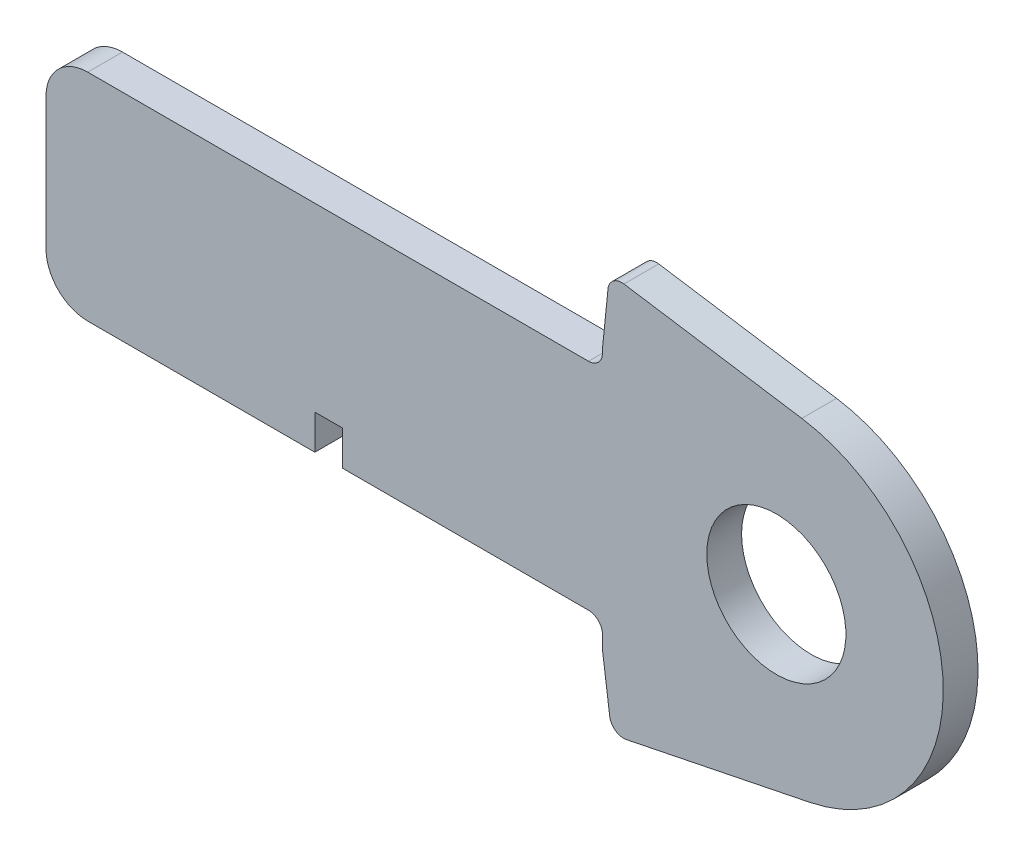
SolidWorks part; units mm, degrees
ref_plane "Front Plane" through (0, 0, 0) normal (0, 0, 1) x (1, 0, 0)
ref_plane "Top Plane" through (0, 0, 0) normal (0, 1, 0) x (1, 0, 0)
ref_plane "Right Plane" through (0, 0, 0) normal (1, 0, 0) x (0, 0, -1)
curve "Curve1"
  spline degree 3 poles (452.1031, 0.7048, 0) (452.0685, 0.7262, 0) (451.9301, 0.8117, 0) (451.6183, 1.003, 0) (451.099, 1.3216, 0) (450.372, 1.7653, 0) (449.438, 2.3329, 0) (448.2963, 3.0204, 0) (446.9478, 3.8257, 0) (445.3928, 4.7448, 0) (443.6314, 5.7736, 0) (441.6643, 6.9077, 0) (439.4916, 8.1409, 0) (437.1143, 9.468, 0) (434.5331, 10.8828, 0) (431.7485, 12.3789, 0) (428.7615, 13.9486, 0) (425.5733, 15.5853, 0) (422.1844, 17.2798, 0) (418.5964, 19.0251, 0) (414.8106, 20.8125, 0) (410.8282, 22.6325, 0) (406.6515, 24.4776, 0) (402.2816, 26.3365, 0) (397.7212, 28.201, 0) (392.972, 30.0605, 0) (388.0369, 31.9065, 0) (382.9178, 33.7272, 0) (377.6186, 35.5144, 0) (372.1418, 37.2567, 0) (366.4913, 38.9446, 0) (360.6704, 40.5671, 0) (354.684, 42.1159, 0) (348.5359, 43.5797, 0) (342.2312, 44.9487, 0) (335.775, 46.2147, 0) (329.1727, 47.3651, 0) (322.4425, 48.3989, 0) (315.6929, 49.2588, 0) (308.9571, 50.1023, 0) (302.2314, 50.8946, 0) (295.4235, 51.6533, 0) (288.5399, 52.3742, 0) (281.5875, 53.055, 0) (274.5733, 53.6928, 0) (267.5046, 54.2857, 0) (260.3883, 54.8303, 0) (253.2318, 55.3259, 0) (246.0422, 55.768, 0) (238.8272, 56.1563, 0) (231.5941, 56.4881, 0) (224.3504, 56.7611, 0) (217.1039, 56.9737, 0) (209.862, 57.1238, 0) (202.6326, 57.2105, 0) (195.4232, 57.2315, 0) (188.2416, 57.1863, 0) (181.0954, 57.0734, 0) (173.9924, 56.8912, 0) (166.9401, 56.6395, 0) (159.9462, 56.3182, 0) (153.0184, 55.9248, 0) (146.164, 55.4618, 0) (139.3909, 54.9271, 0) (132.7063, 54.3206, 0) (126.1174, 53.645, 0) (119.6314, 52.8983, 0) (113.2554, 52.0826, 0) (106.9962, 51.1996, 0) (100.8609, 50.2488, 0) (94.8561, 49.2329, 0) (88.9882, 48.153, 0) (83.2635, 47.0122, 0) (77.6882, 45.8109, 0) (72.2682, 44.5525, 0) (67.0092, 43.2395, 0) (61.9167, 41.874, 0) (56.9959, 40.4594, 0) (52.2519, 38.999, 0) (47.6902, 37.4943, 0) (43.3141, 35.951, 0) (39.1291, 34.3702, 0) (35.1384, 32.7568, 0) (31.3466, 31.113, 0) (27.7567, 29.4439, 0) (24.3726, 27.7512, 0) (21.1967, 26.0397, 0) (18.2324, 24.3122, 0) (15.4823, 22.5717, 0) (12.9477, 20.8227, 0) (10.632, 19.0664, 0) (8.5361, 17.307, 0) (6.6613, 15.5474, 0) (5.0102, 13.7886, 0) (3.5829, 12.0339, 0) (2.3811, 10.2847, 0) (1.4051, 8.5424, 0) (0.6571, 6.8085, 0) (0.1363, 5.084, 0) (-0.1488, 3.3712, 0) (-0.2197, 1.669, 0) (-0.0731, 0.5555, 0) (0, 0, 0) knots 0 0 0 0 0.000254 0.001015 0.002283 0.004057 0.006331 0.009105 0.012374 0.016134 0.02038 0.025106 0.030306 0.035972 0.0421 0.048678 0.055702 0.06316 0.071046 0.07935 0.088063 0.097176 0.106678 0.116562 0.126814 0.137428 0.148394 0.1597 0.171338 0.183298 0.19557 0.208144 0.221012 0.234162 0.247587 0.261277 0.275223 0.289414 0.303771 0.317689 0.331784 0.34604 0.360444 0.374983 0.38964 0.404403 0.419257 0.434187 0.449177 0.464215 0.479284 0.49437 0.509458 0.524532 0.539579 0.554583 0.56953 0.584403 0.599191 0.613877 0.628447 0.642889 0.657186 0.671326 0.685294 0.699078 0.712665 0.726043 0.739198 0.752118 0.764792 0.777208 0.789356 0.801224 0.812804 0.824083 0.835055 0.84571 0.856038 0.866034 0.875689 0.884998 0.893953 0.902553 0.910789 0.918661 0.926166 0.933303 0.940071 0.946475 0.952518 0.958205 0.963547 0.968557 0.97325 0.977651 0.981787 0.985694 0.989415 0.993001 0.996508 1 1 1 1
curve "Curve2"
  spline degree 3 poles (0, 0, 0) (0.1161, -0.5481, 0) (0.3488, -1.6467, 0) (0.9811, -3.2283, 0) (1.8173, -4.7487, 0) (2.8749, -6.2038, 0) (4.147, -7.5932, 0) (5.6306, -8.9184, 0) (7.3243, -10.1787, 0) (9.226, -11.3735, 0) (11.3328, -12.5041, 0) (13.6425, -13.5697, 0) (16.1528, -14.5701, 0) (18.8611, -15.5039, 0) (21.764, -16.3724, 0) (24.8588, -17.1737, 0) (28.1419, -17.9088, 0) (31.6103, -18.5759, 0) (35.26, -19.1755, 0) (39.0874, -19.7075, 0) (43.0885, -20.172, 0) (47.2594, -20.5682, 0) (51.596, -20.8969, 0) (56.0938, -21.1583, 0) (60.7487, -21.3533, 0) (65.556, -21.481, 0) (70.5112, -21.5436, 0) (75.6096, -21.5419, 0) (80.8464, -21.4754, 0) (86.2171, -21.3479, 0) (91.7164, -21.1586, 0) (97.3395, -20.9096, 0) (103.0813, -20.6036, 0) (108.9365, -20.2416, 0) (114.9002, -19.8251, 0) (120.967, -19.3576, 0) (127.1315, -18.8401, 0) (133.3883, -18.2757, 0) (139.7319, -17.6673, 0) (146.1567, -17.0167, 0) (152.6572, -16.327, 0) (159.2275, -15.6004, 0) (165.862, -14.8409, 0) (172.5546, -14.0497, 0) (179.2998, -13.2315, 0) (186.0911, -12.3877, 0) (192.923, -11.5217, 0) (199.7891, -10.6375, 0) (206.6832, -9.7349, 0) (213.5994, -8.8205, 0) (220.5311, -7.8935, 0) (227.4721, -6.9586, 0) (234.4161, -6.0188, 0) (241.3564, -5.0743, 0) (248.2868, -4.1291, 0) (255.2009, -3.1857, 0) (262.0918, -2.2442, 0) (268.9535, -1.3094, 0) (275.779, -0.3811, 0) (282.5619, 0.5389, 0) (289.2958, 1.4477, 0) (295.9744, 2.3443, 0) (302.5907, 3.228, 0) (309.138, 4.0992, 0) (315.5119, 4.9314, 0) (321.6955, 5.769, 0) (327.7099, 6.4556, 0) (333.6493, 7.0417, 0) (339.52, 7.5222, 0) (345.315, 7.9041, 0) (351.0275, 8.19, 0) (356.6509, 8.3839, 0) (362.1779, 8.4917, 0) (367.6017, 8.516, 0) (372.9148, 8.4647, 0) (378.1105, 8.3417, 0) (383.1813, 8.1528, 0) (388.1203, 7.9042, 0) (392.9205, 7.6027, 0) (397.5745, 7.2527, 0) (402.076, 6.8625, 0) (406.4179, 6.4377, 0) (410.5937, 5.9833, 0) (414.5972, 5.5086, 0) (418.4221, 5.0169, 0) (422.0625, 4.5163, 0) (425.5126, 4.0117, 0) (428.7669, 3.5097, 0) (431.8204, 3.015, 0) (434.6681, 2.5342, 0) (437.3055, 2.0718, 0) (439.7281, 1.6323, 0) (441.9324, 1.2212, 0) (443.9143, 0.8406, 0) (445.6709, 0.4968, 0) (447.199, 0.1913, 0) (448.4964, -0.0716, 0) (449.5609, -0.2909, 0) (450.3908, -0.463, 0) (450.9844, -0.5881, 0) (451.3411, -0.6626, 0) (451.4997, -0.6964, 0) (451.5393, -0.7048, 0) knots 0 0 0 0 0.003638 0.007293 0.011028 0.014901 0.018963 0.023258 0.027821 0.032679 0.037853 0.043362 0.049215 0.055422 0.061989 0.068918 0.076211 0.083868 0.091887 0.100266 0.109 0.118085 0.127515 0.137285 0.147388 0.157816 0.168563 0.179619 0.190977 0.202627 0.21456 0.226767 0.239236 0.251959 0.264924 0.27812 0.291536 0.30516 0.318981 0.332985 0.347163 0.361499 0.375981 0.390597 0.405333 0.420175 0.43511 0.450124 0.465203 0.480333 0.495501 0.51069 0.525887 0.541078 0.556247 0.571382 0.586466 0.601485 0.616424 0.631269 0.646007 0.660621 0.675098 0.689423 0.703582 0.716908 0.730009 0.742952 0.755726 0.76832 0.780724 0.792927 0.804916 0.816679 0.828204 0.839475 0.850481 0.861208 0.871639 0.881763 0.891564 0.901027 0.910139 0.918884 0.927249 0.935221 0.942785 0.949928 0.956638 0.962904 0.968712 0.974054 0.978918 0.983297 0.98718 0.990561 0.993433 0.995791 0.99763 0.998946 0.999737 1 1 1 1
sketch "Sketch1" plane through (0, 0, 0) normal (0, 0, 1) x (1, 0, 0)
  line L24 (435.3301, 0.6787) -> (439.1729, -1.6142)
  line L25 (434.7872, -0.6787) -> (439.1729, -1.6142)
  spline S4 degree 3 poles (0, 0) (0.1118, -0.5277) (0.3359, -1.5856) (0.9447, -3.1085) (1.7499, -4.5725) (2.7683, -5.9736) (3.9931, -7.3115) (5.4217, -8.5876) (7.0526, -9.8011) (8.8837, -10.9516) (10.9124, -12.0402) (13.1363, -13.0663) (15.5535, -14.0296) (18.1613, -14.9287) (20.9565, -15.765) (23.9365, -16.5366) (27.0978, -17.2444) (30.4375, -17.8867) (33.9519, -18.4641) (37.6373, -18.9763) (41.49, -19.4236) (45.5061, -19.8051) (49.6818, -20.1216) (54.0128, -20.3734) (58.4949, -20.5611) (63.1239, -20.6841) (67.8952, -20.7443) (72.8045, -20.7427) (77.847, -20.6787) (83.0184, -20.5559) (88.3137, -20.3736) (93.7282, -20.1339) (99.2569, -19.8392) (104.895, -19.4906) (110.6374, -19.0896) (116.4791, -18.6394) (122.4149, -18.1411) (128.4396, -17.5977) (134.5478, -17.0118) (140.7343, -16.3853) (146.9936, -15.7212) (153.3201, -15.0216) (159.7085, -14.2903) (166.1528, -13.5285) (172.6478, -12.7406) (179.1872, -11.9281) (185.7655, -11.0942) (192.377, -10.2428) (199.0153, -9.3738) (205.6749, -8.4933) (212.3494, -7.6007) (219.0329, -6.7005) (225.7193, -5.7955) (232.4021, -4.886) (239.0753, -3.9759) (245.7329, -3.0675) (252.3682, -2.161) (258.9753, -1.2608) (265.5476, -0.3669) (272.0789, 0.5189) (278.563, 1.394) (284.9937, 2.2573) (291.3645, 3.1082) (297.669, 3.9471) (303.8064, 4.7484) (309.7606, 5.555) (315.5518, 6.2161) (321.2709, 6.7805) (326.9238, 7.2431) (332.5038, 7.6108) (338.0044, 7.8861) (343.4191, 8.0729) (348.7411, 8.1767) (353.9637, 8.2001) (359.0797, 8.1506) (364.0826, 8.0323) (368.9653, 7.8503) (373.7211, 7.6109) (378.3431, 7.3206) (382.8245, 6.9836) (387.159, 6.6079) (391.3398, 6.1989) (395.3607, 5.7613) (399.2157, 5.3043) (402.8986, 4.8308) (406.404, 4.3487) (409.7261, 3.8629) (412.8597, 3.3795) (415.7999, 2.9031) (418.5419, 2.4402) (421.0815, 1.9949) (423.4142, 1.5717) (425.5368, 1.1759) (427.445, 0.8095) (429.1365, 0.4784) (430.6079, 0.1842) (431.8572, -0.0689) (432.8822, -0.2801) (433.6813, -0.4458) (434.2529, -0.5663) (434.5964, -0.638) (434.749, -0.6706) (434.7872, -0.6787) knots 0 0 0 0 0.003638 0.007293 0.011028 0.014901 0.018963 0.023258 0.027821 0.032679 0.037853 0.043362 0.049215 0.055422 0.061989 0.068918 0.076211 0.083868 0.091887 0.100266 0.109 0.118085 0.127515 0.137285 0.147388 0.157816 0.168563 0.179619 0.190977 0.202627 0.21456 0.226767 0.239236 0.251959 0.264924 0.27812 0.291536 0.30516 0.318981 0.332985 0.347163 0.361499 0.375981 0.390597 0.405333 0.420175 0.43511 0.450124 0.465203 0.480333 0.495501 0.51069 0.525887 0.541078 0.556247 0.571382 0.586466 0.601485 0.616424 0.631269 0.646007 0.660621 0.675098 0.689423 0.703582 0.716908 0.730009 0.742952 0.755726 0.76832 0.780724 0.792927 0.804916 0.816679 0.828204 0.839475 0.850481 0.861208 0.871639 0.881763 0.891564 0.901027 0.910139 0.918884 0.927249 0.935221 0.942785 0.949928 0.956638 0.962904 0.968712 0.974054 0.978918 0.983297 0.98718 0.990561 0.993433 0.995791 0.99763 0.998946 0.999737 1 1 1 1
  spline S5 degree 3 poles (435.3301, 0.6787) (435.2968, 0.6993) (435.1635, 0.7816) (434.8632, 0.9658) (434.3632, 1.2726) (433.6632, 1.6998) (432.7638, 2.2463) (431.6645, 2.9084) (430.3661, 3.6837) (428.8687, 4.5688) (427.1727, 5.5594) (425.2785, 6.6514) (423.1865, 7.8389) (420.8974, 9.1168) (418.4119, 10.4791) (415.7306, 11.9197) (412.8545, 13.4311) (409.7845, 15.0071) (406.5213, 16.6387) (403.0665, 18.3192) (399.4211, 20.0403) (395.5865, 21.7928) (391.5647, 23.5695) (387.357, 25.3594) (382.9657, 27.1547) (378.3927, 28.9452) (373.6407, 30.7228) (368.7116, 32.4759) (363.609, 34.1968) (358.3353, 35.8745) (352.8945, 37.4998) (347.2896, 39.0621) (341.5252, 40.5534) (335.6052, 41.9629) (329.5344, 43.2811) (323.3177, 44.5002) (316.9603, 45.6079) (310.4799, 46.6033) (303.9807, 47.4313) (297.4948, 48.2435) (291.0186, 49.0064) (284.4633, 49.737) (277.8351, 50.4311) (271.1406, 51.0867) (264.3866, 51.7008) (257.5802, 52.2717) (250.7279, 52.7961) (243.8369, 53.2733) (236.914, 53.699) (229.9667, 54.0729) (223.0019, 54.3924) (216.027, 54.6553) (209.0493, 54.86) (202.0761, 55.0045) (195.1149, 55.088) (188.173, 55.1082) (181.2578, 55.0647) (174.3767, 54.956) (167.5373, 54.7806) (160.7467, 54.5381) (154.0122, 54.2288) (147.3414, 53.85) (140.7414, 53.4041) (134.2195, 52.8893) (127.7829, 52.3053) (121.4385, 51.6548) (115.1931, 50.9357) (109.0536, 50.1503) (103.0266, 49.3001) (97.119, 48.3846) (91.3369, 47.4064) (85.6868, 46.3665) (80.1745, 45.2681) (74.806, 44.1113) (69.5871, 42.8996) (64.5231, 41.6353) (59.6196, 40.3205) (54.8814, 38.9584) (50.3134, 37.5521) (45.9209, 36.1032) (41.7071, 34.6172) (37.6774, 33.0951) (33.8348, 31.5415) (30.1837, 29.9587) (26.7269, 28.3515) (23.4684, 26.7216) (20.4104, 25.0737) (17.5559, 23.4102) (14.9079, 21.7343) (12.4673, 20.0502) (10.2376, 18.359) (8.2194, 16.6649) (6.4142, 14.9706) (4.8244, 13.2771) (3.45, 11.5875) (2.2928, 9.9031) (1.353, 8.2255) (0.6327, 6.5559) (0.1312, 4.8953) (-0.1433, 3.2462) (-0.2116, 1.607) (-0.0704, 0.5349) (0, 0) knots 0 0 0 0 0.000254 0.001015 0.002283 0.004057 0.006331 0.009105 0.012374 0.016134 0.02038 0.025106 0.030306 0.035972 0.0421 0.048678 0.055702 0.06316 0.071046 0.07935 0.088063 0.097176 0.106678 0.116562 0.126814 0.137428 0.148394 0.1597 0.171338 0.183298 0.19557 0.208144 0.221012 0.234162 0.247587 0.261277 0.275223 0.289414 0.303771 0.317689 0.331784 0.34604 0.360444 0.374983 0.38964 0.404403 0.419257 0.434187 0.449177 0.464215 0.479284 0.49437 0.509458 0.524532 0.539579 0.554583 0.56953 0.584403 0.599191 0.613877 0.628447 0.642889 0.657186 0.671326 0.685294 0.699078 0.712665 0.726043 0.739198 0.752118 0.764792 0.777208 0.789356 0.801224 0.812804 0.824083 0.835055 0.84571 0.856038 0.866034 0.875689 0.884998 0.893953 0.902553 0.910789 0.918661 0.926166 0.933303 0.940071 0.946475 0.952518 0.958205 0.963547 0.968557 0.97325 0.977651 0.981787 0.985694 0.989415 0.993001 0.996508 1 1 1 1
extrude "Boss-Extrude1" add sketch "Sketch1" along normal blind 3.175
sketch "Sketch2" plane through (0, 0, 0) normal (0, 0, -1) x (-1, 0, 0)
  line L0 (-252.7944, 13.2215) -> (-250.2544, 13.2215)
  line L1 (-250.2544, -2.1152) -> (-250.2544, -3.9863)
  line L2 (-252.7944, 13.2215) -> (-252.7944, -2.1152)
  line L4 (-250.2544, -3.9863) -> (-252.7944, -3.0508)
  line L5 (-252.7944, -3.0508) -> (-252.7944, -2.1152)
  line L7 (-159.1319, 54.4222) -> (-159.1319, 39.0391)
  line L8 (-159.1319, 39.0391) -> (-152.7819, 39.0391)
  line L9 (-152.7819, 54.4222) -> (-152.7819, 57.6454)
  line L10 (-74.9944, -5.9288) -> (-74.9944, -20.1418)
  line L12 (-152.7819, 57.6454) -> (-159.1319, 55.5409)
  line L13 (-159.1319, 55.5409) -> (-159.1319, 54.4222)
  line L14 (-71.8194, -5.9288) -> (-71.8194, -20.1418)
  line L16 (-74.9944, -5.9288) -> (-71.8194, -5.9288)
  line L17 (-71.8194, -20.1418) -> (-71.8194, -22.1459)
  line L19 (-152.7819, 54.4222) -> (-152.7819, 39.0391)
  line L20 (-71.8194, -22.1459) -> (-74.9944, -20.9764)
  line L21 (-74.9944, -20.9764) -> (-74.9944, -20.1418)
  line L22 (-250.2544, 13.2215) -> (-250.2544, -2.1152)
extrude "Cut-Extrude1" cut sketch "Sketch2" against normal blind 7.62
sketch "Sketch3" plane through (0, 0, 0) normal (0, 0, -1) x (-1, 0, 0)
  circle A1 centre (-292.3838, 26.2554) radius 6.35
extrude "Cut-Extrude2" cut sketch "Sketch3" against normal blind 7.62
sketch "Sketch4" plane through (0, 0, 3.175) normal (0, 0, 1) x (1, 0, 0)
  line L0 (274.6066, 50.6647) -> (273.3497, 38.0281)
  line L1 (274.6066, 50.6647) -> (273.3497, 38.0281)
  line L2 (276.5088, 37.7139) -> (277.7874, 50.3428)
  line L3 (276.5088, 37.7139) -> (277.7874, 50.3428)
  line L4 (278.2022, 1.3477) -> (276.5088, 13.9346)
  line L5 (278.2022, 1.3477) -> (276.5088, 13.9346)
  line L6 (273.3622, 13.5108) -> (275.0576, 0.9245)
  line L7 (273.3622, 13.5108) -> (275.0576, 0.9245)
  line L14 (277.1481, 44.0283) -> (294.7093, 41.317)
  line L22 (225.7088, 36.0979) -> (276.5088, 36.0979)
  line L24 (225.7088, 36.0979) -> (225.7088, 16.4129)
  line L26 (225.7088, 16.4129) -> (276.5088, 16.4129)
  line L32 (277.3555, 7.6412) -> (295.4257, 11.3221)
  line L34 (276.5088, 13.9346) -> (276.5088, 37.7139)
  line L35 (273.3497, 38.0281) -> (276.5088, 37.7139)
  line L36 (276.5088, 13.9346) -> (273.3622, 13.5108)
  line L37 (275.0576, 0.9245) -> (278.2022, 1.3477)
  line L49 (277.7874, 50.3428) -> (274.6066, 50.6647)
  line L50 (250.2544, 13.2215) -> (250.2544, 19.5879)
  line L51 (225.7088, 31.0179) -> (263.8088, 31.0179)
  line L52 (225.7088, 31.0179) -> (225.7088, 21.4929)
  line L53 (225.7088, 21.4929) -> (263.8088, 21.4929)
  line L54 (263.8088, 31.0179) -> (263.8088, 21.4929)
  line L55 (250.2544, 19.5879) -> (252.7944, 19.5879)
  line L56 (252.7944, 19.5879) -> (252.7944, 13.2215)
  circle A0 centre (292.3838, 26.2554) radius 6.35 construction
  circle A1 centre (292.3838, 26.2554) radius 6.35
  circle A2 centre (292.3838, 26.2554) radius 15.24
  point P12 (225.7088, 26.2554)
  point P13 (225.7088, 26.2554)
  point P40 (263.8088, 26.2554)
  dimension "D6" = 30.48
  dimension "D1" = 9.525
  dimension "D2" = 38.1
  dimension "D3" = 12.7
  dimension "D4" = 5.08
  dimension "D5" = 3.175
extrude "Cut-Extrude3" cut sketch "Sketch4" against normal through all
fillet "Fillet1" radius 3.81 2 edges at (225.7088, 16.4129, 1.5875) (225.7088, 36.0979, 1.5875)
fillet "Fillet2" radius 1.27 4 edges at (277.3555, 7.6412, 1.5875) (277.1481, 44.0283, 1.5875) (276.5088, 16.4129, 1.5875) (276.5088, 36.0979, 1.5875)
